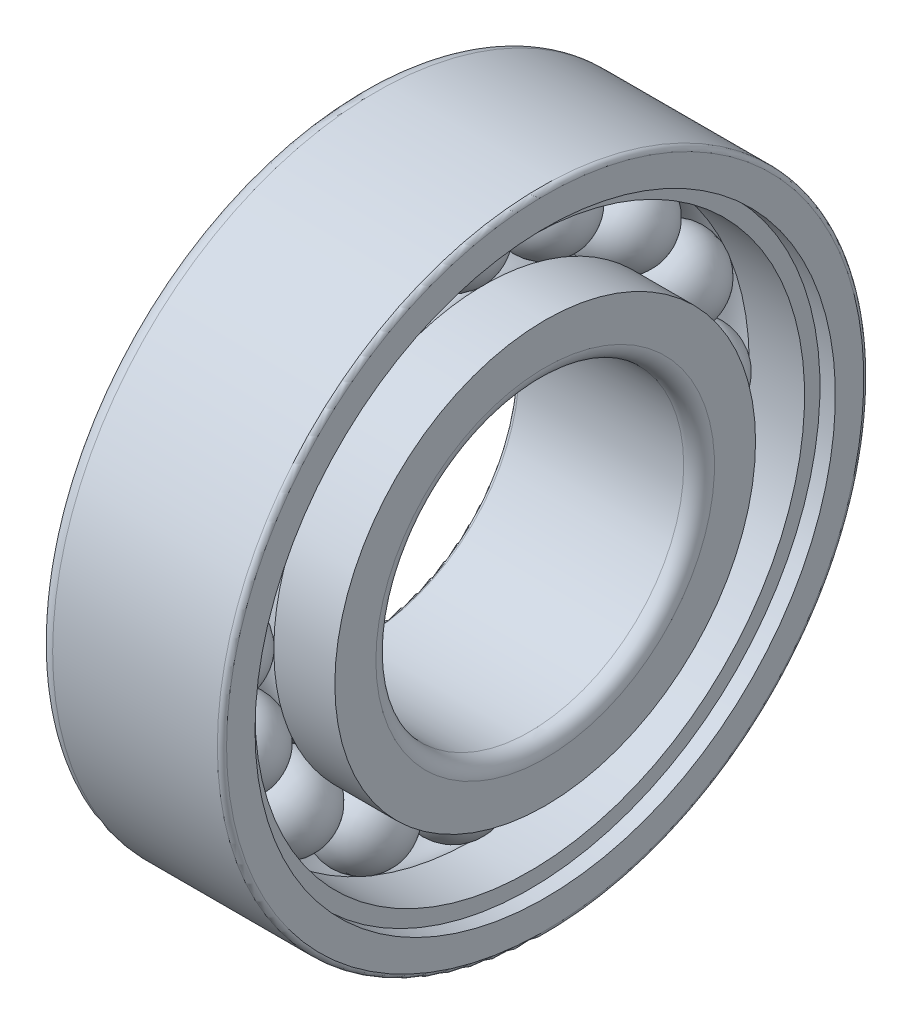
SolidWorks part; units mm, degrees
ref_plane "Front" through (0, 0, 0) normal (0, 0, 1) x (1, 0, 0)
ref_plane "Top" through (0, 0, 0) normal (0, 1, 0) x (1, 0, 0)
ref_plane "Right" through (0, 0, 0) normal (1, 0, 0) x (0, 0, -1)
sketch "Sketch1" plane through (0, 0, 0) normal (0, 0, 1) x (1, 0, 0)
  line L0 (-3.0919, 0) -> (2.899, 0) construction
  line L1 (-3.0919, 15.5) -> (2.899, 15.5) construction
  line L2 (-2.75, 15.5) -> (2.75, 15.5)
  arc A0 (-2.75, 15.5) -> (2.75, 15.5) centre (0, 15.5) ccw
  dimension "R" = 2.75
  dimension "D1" = 15.5
revolve "Revolve1" add sketch "Sketch1" angle 360 about L1
sketch "Sketch2" plane through (0, 0, 0) normal (0, 0, 1) x (1, 0, 0)
  line L0 (-6, 13.6667) -> (-2.0363, 13.6667)
  line L1 (6, 13.6667) -> (6, 10)
  line L2 (6, 10) -> (-6, 10)
  line L3 (-6, 10) -> (-6, 13.6667)
  line L4 (-2.9924, 0) -> (3.9982, 0) construction
  line L5 (-1.8743, 15.5) -> (3.1755, 15.5) construction
  line L7 (2.0363, 13.6667) -> (6, 13.6667)
  line L8 (-6, 6.2861) -> (-6, 1.454) construction
  arc A0 (-2.0363, 13.6667) -> (2.0363, 13.6667) centre (0, 15.5) ccw
  dimension "D2" = 2.74
  dimension "D1" = 15.5
  dimension "d" = 20
  dimension "D3" = 27.3333
  dimension "T" = 12
  dimension "D6" = 6
  dimension "B" = 12
revolve "Revolve2" add sketch "Sketch2" angle 360 about L4
sketch "Sketch3" plane through (0, 0, 0) normal (0, 0, 1) x (1, 0, 0)
  line L0 (-6, 17.3333) -> (-6, 21)
  line L1 (-6, 21) -> (6, 21)
  line L2 (6, 21) -> (6, 18.8533)
  line L3 (5, 17.8533) -> (1.4034, 17.8533)
  line L4 (-2.9924, 0) -> (3.4329, 0) construction
  line L6 (-1.7375, 15.5) -> (2.2712, 15.5) construction
  line L7 (-2.0363, 17.3333) -> (-6, 17.3333)
  line L8 (5, 17.8533) -> (5, 18.8533)
  line L9 (5, 18.8533) -> (6, 18.8533)
  arc A0 (1.4034, 17.8533) -> (-2.0363, 17.3333) centre (0, 15.5) ccw
  dimension "D4" = 2.74
  dimension "D1" = 15.5
  dimension "D2" = 6
  dimension "B" = 12
  dimension "D3" = 35.7067
  dimension "DD" = 42
  dimension "D5" = 34.6667
  dimension "D6" = 1
  dimension "D7" = 1
revolve "Revolve3" add sketch "Sketch3" angle 360 about L4
pattern_circular "Circular-Pattern1" count 16 over 360 about axis through (0, 0, 0) along (1, 0, 0) of "Revolve1"
fillet "Fillet1" radius 1 2 edges at (6, 0, 10) (-6, 0, 21)
fillet "Fillet2" radius 0.3 2 edges at (6, 0, 21) (-6, 0, 10)
equation "\"R@Sketch1\" =  ( \"DD@Sketch3\" - \"d@Sketch2\" )  / 8"
equation "\"D1@Sketch1\"=(\"d@Sketch2\"+\"DD@Sketch3\")/4"
equation "\"D1@Sketch2\"=(\"d@Sketch2\"+\"DD@Sketch3\")/4"
equation "\"D3@Sketch2\" =  \"d@Sketch2\"+  ( \"DD@Sketch3\" - \"d@Sketch2\" )  /3"
equation "\"D2@Sketch2\" =  ( \"DD@Sketch3\" - \"d@Sketch2\" )  / 8 - 0.01"
equation "\"D6@Sketch2\" = \"B@Sketch2\" / 2"
equation "\"B@Sketch3\" = \"B@Sketch2\""
equation "\"D2@Sketch3\" = \"B@Sketch3\" / 2"
equation "\"D1@Sketch3\"=(\"d@Sketch2\"+\"DD@Sketch3\")/4"
equation "\"D3@Sketch3\" = (  \"DD@Sketch3\" -  (\"DD@Sketch3\" - \"d@Sketch2\"  )  / 3 )  * 1.03"
equation "\"D5@Sketch3\" = \"DD@Sketch3\" -  (  \"DD@Sketch3\" - \"d@Sketch2\")  / 3"
equation "\"D6@Sketch3\" = \"d@Sketch2\" / 20"
equation "\"D7@Sketch3\"=\"D6@Sketch3\""
equation "\"D4@Sketch3\"=(\"DD@Sketch3\"-\"d@Sketch2\")/8-0.01"
equation "\"m@Circular-Pattern1\" = int( 3.14159265 / atn(\"R@Sketch1\" / sqr((\"d@Sketch2\"+\"DD@Sketch3\")/4 * (\"d@Sketch2\"+\"DD@Sketch3\")/4 - \"R@Sketch1\" *  \"R@Sketch1\")))-1"
